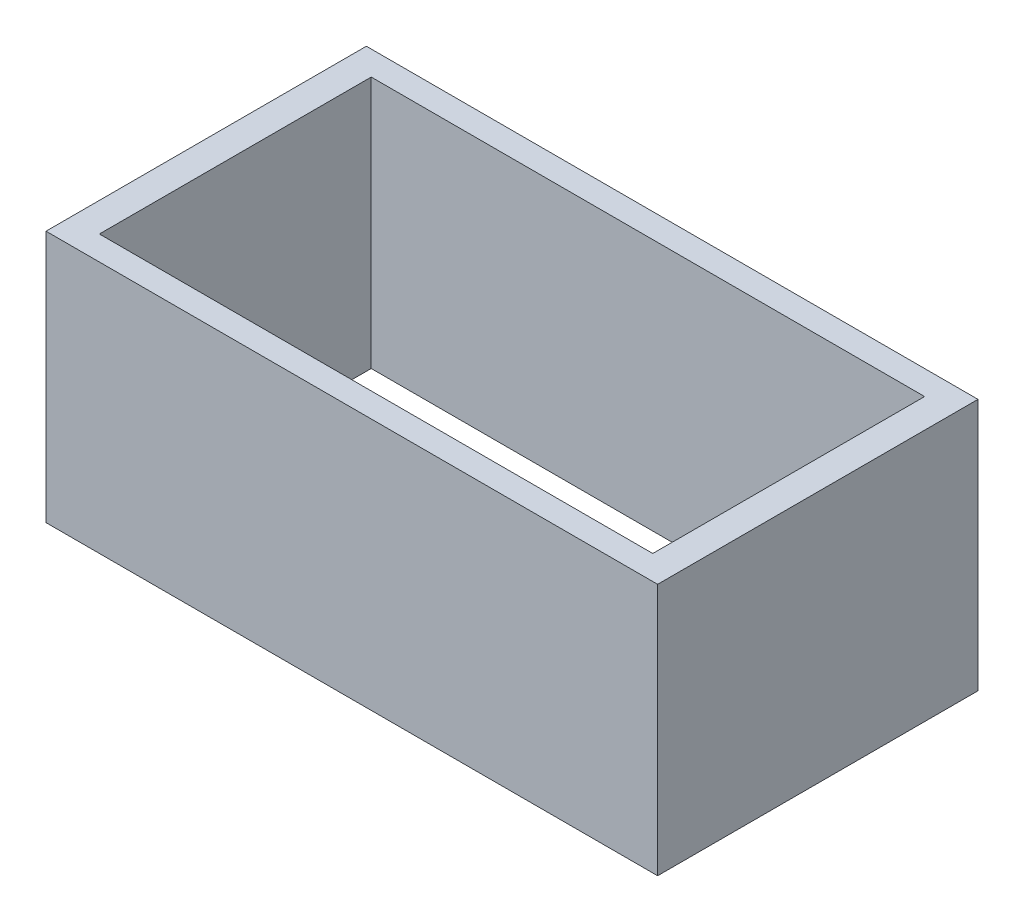
SolidWorks part; units mm, degrees
ref_plane "Front Plane" through (0, 0, 0) normal (0, 0, 1) x (1, 0, 0)
ref_plane "Top Plane" through (0, 0, 0) normal (0, 1, 0) x (1, 0, 0)
ref_plane "Right Plane" through (0, 0, 0) normal (1, 0, 0) x (0, 0, -1)
sketch "Sketch1" plane through (0, 0, 0) normal (0, 1, 0) x (1, 0, 0)
  line L0 (0, 0) -> (-14.25, 0) construction
  line L1 (10.75, 5) -> (-10.75, 5)
  line L2 (10.75, 5) -> (10.75, -5) construction
  line L3 (10.75, -5) -> (-10.75, -5)
  line L4 (-10.75, 7) -> (-10.75, 5)
  line L5 (10.75, 5) -> (-10.75, -5) construction
  line L6 (10.75, -5) -> (-10.75, 5) construction
  line L7 (-10.75, -7) -> (-14.25, -7)
  line L8 (-10.75, -7) -> (-10.75, -5)
  line L9 (-10.75, 7) -> (-14.25, 7)
  line L10 (-14.25, -7) -> (-14.25, 7)
  line L12 (15.75, -8.25) -> (-15.75, -8.25)
  line L13 (-10.75, 5) -> (-10.75, -5) construction
  line L14 (0, 0) -> (14.25, 0) construction
  line L15 (10.75, -7) -> (14.25, -7)
  line L16 (10.75, 7) -> (10.75, 5)
  line L17 (10.75, 7) -> (14.25, 7)
  line L18 (14.25, -7) -> (14.25, 7)
  line L19 (10.75, -5) -> (10.75, -7)
  line L20 (15.75, -8.25) -> (15.75, 8.25)
  line L21 (15.75, 8.25) -> (-15.75, 8.25)
  line L22 (-15.75, -8.25) -> (-15.75, 8.25)
  line L23 (15.75, -8.25) -> (-15.75, 8.25) construction
  line L24 (15.75, 8.25) -> (-15.75, -8.25) construction
  point P0 (0, 0)
  dimension "D1" = 10
  dimension "D2" = 21.5
  dimension "D5" = 14
  dimension "D6" = 3.5
  dimension "D7" = 1.5
  dimension "D8" = 16.5
extrude "Boss-Extrude1" add sketch "Sketch1" along normal blind 13
sketch "Sketch2" plane through (0, 0, 0) normal (0, -1, 0) x (1, 0, 0)
  line L1 (10.75, 7) -> (-10.75, 7)
  line L2 (10.75, 7) -> (10.75, 5)
  line L3 (10.75, 5) -> (-10.75, 5)
  line L4 (-10.75, 7) -> (-10.75, 5)
  line L5 (10.75, 7) -> (-10.75, 5) construction
  line L6 (10.75, 5) -> (-10.75, 7) construction
  line L7 (10.75, -7) -> (-10.75, -7)
  line L8 (10.75, -7) -> (10.75, -5)
  line L9 (10.75, -5) -> (-10.75, -5)
  line L10 (-10.75, -7) -> (-10.75, -5)
  line L11 (10.75, -7) -> (-10.75, -5) construction
  line L12 (10.75, -5) -> (-10.75, -7) construction
  point P0 (0, 6)
  point P6 (0, -6)
extrude "Cut-Extrude1" cut sketch "Sketch2" against normal through all
